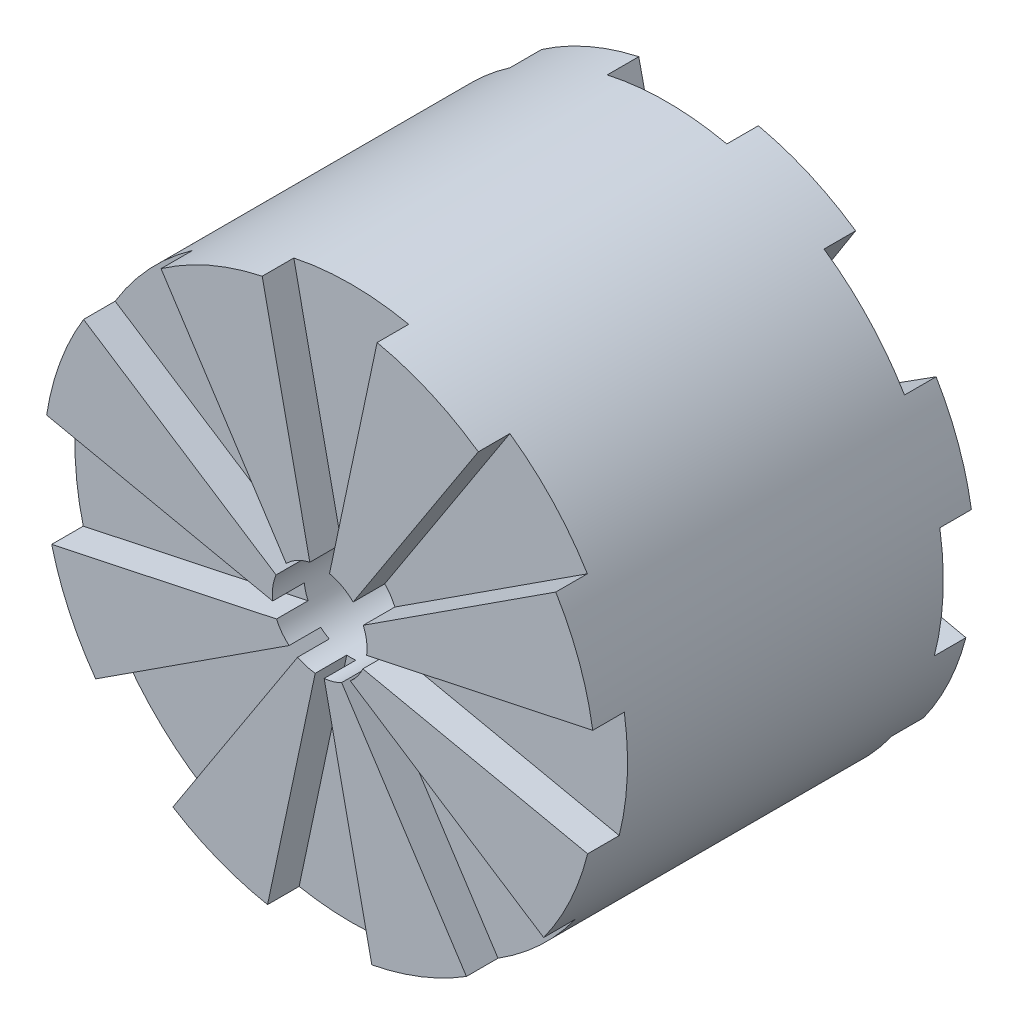
SolidWorks part; units mm, degrees
material "Ductile Iron"
ref_plane "Front Plane" through (0, 0, 0) normal (0, 0, 1) x (1, 0, 0)
ref_plane "Top Plane" through (0, 0, 0) normal (0, 1, 0) x (1, 0, 0)
ref_plane "Right Plane" through (0, 0, 0) normal (1, 0, 0) x (0, 0, -1)
sketch "Sketch1" plane through (0, 0, 0) normal (0, 0, 1) x (1, 0, 0)
  circle A0 centre (0, 0) radius 87.5
  dimension "D1" = 175
extrude "Boss-Extrude1" add sketch "Sketch1" along normal blind 120
sketch "Sketch2" plane through (0, 0, 120) normal (0, 0, 1) x (1, 0, 0)
  line L0 (0, 0) -> (18.1923, 85.5879)
  line L1 (0, 0) -> (-18.1923, 85.5879)
  line L2 (0, 0) -> (0, 113.3296) construction
  circle A0 centre (0, 0) radius 87.5 construction
  circle A1 centre (0, 0) radius 87.5
  circle A2 centre (0, 0) radius 87.5
  circle M5 centre (0, 0) radius 87.5
  dimension "D1" = 24
extrude "Cut-Extrude1" cut sketch "Sketch2" against normal blind 10 contours L1 L2 A2 | L2 L0 M5
ref_plane "Plane1" through (0, 120, 0) normal (0, 1, 0) x (1, 0, 0)
pattern_circular "CirPattern1" count 8 over 360 about axis through (0, -4.1363, 0) along (0, 0, 1) of "Cut-Extrude1"
sketch "Sketch4" plane through (0, 0, 0) normal (0, 0, -1) x (-1, 0, 0)
  line L0 (0, 0) -> (18.9385, 85.4259)
  line L1 (0, 0) -> (-18.9385, 85.4259)
  line L2 (0, 0) -> (0, 117.7066) construction
  circle A0 centre (0, 0) radius 87.5 construction
  circle A1 centre (0, 0) radius 87.5
  circle M4 centre (0, 0) radius 87.5
  dimension "D1" = 25
extrude "Cut-Extrude2" cut sketch "Sketch4" against normal blind 10 contours L1 L2 A1 | L2 L0 M4
pattern_circular "CirPattern2" count 8 over 360 about axis through (0, -4.3188, 0) along (0, 0, 1) of "Cut-Extrude2"
sketch "Sketch5" plane through (0, 0, 120) normal (0, 0, 1) x (1, 0, 0)
  circle A0 centre (0, 0) radius 15
  dimension "D1" = 30
extrude "Cut-Extrude3" cut sketch "Sketch5" against normal through all
